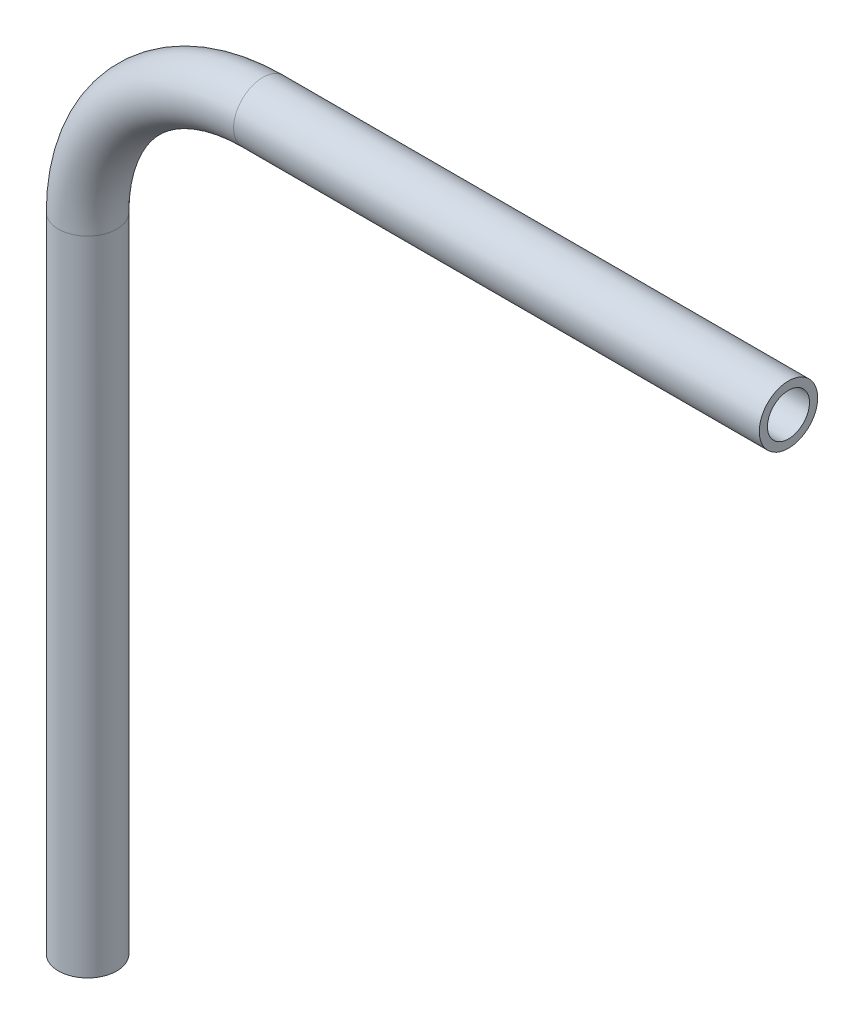
SolidWorks part; units mm, degrees
material "AISI 316 Stainless Steel Sheet (SS)"
ref_plane "Front Plane" through (0, 0, 0) normal (0, 0, 1) x (1, 0, 0)
ref_plane "Top Plane" through (0, 0, 0) normal (0, 1, 0) x (1, 0, 0)
ref_plane "Right Plane" through (0, 0, 0) normal (1, 0, 0) x (0, 0, -1)
sketch "Sketch1" plane through (0, 0, 0) normal (0, 0, 1) x (1, 0, 0)
  line L0 (0, -71.3723) -> (0, -1.5223)
  line L1 (19.05, 17.5277) -> (76.2, 17.5277)
  arc A0 (0, -1.5223) -> (19.05, 17.5277) centre (19.05, -1.5223) cw
  point P6 (0, 17.5277)
  dimension "D3" = 19.05
  dimension "D1" = 76.2
  dimension "D2" = 88.9
ref_plane "Plane1" through (76.2, 17.5277, 0) normal (1, 0, 0) x (0, 0, -1)
sketch "Sketch2" plane through (76.2, 17.5277, 0) normal (1, 0, 0) x (0, 0, -1)
  circle A0 centre (0, 0) radius 3.175
  circle A1 centre (0, 0) radius 2.286
  dimension "D1" = 6.35
  dimension "D2" = 4.572
sweep "Sweep1" add profiles "Sketch2" path "Sketch1"
